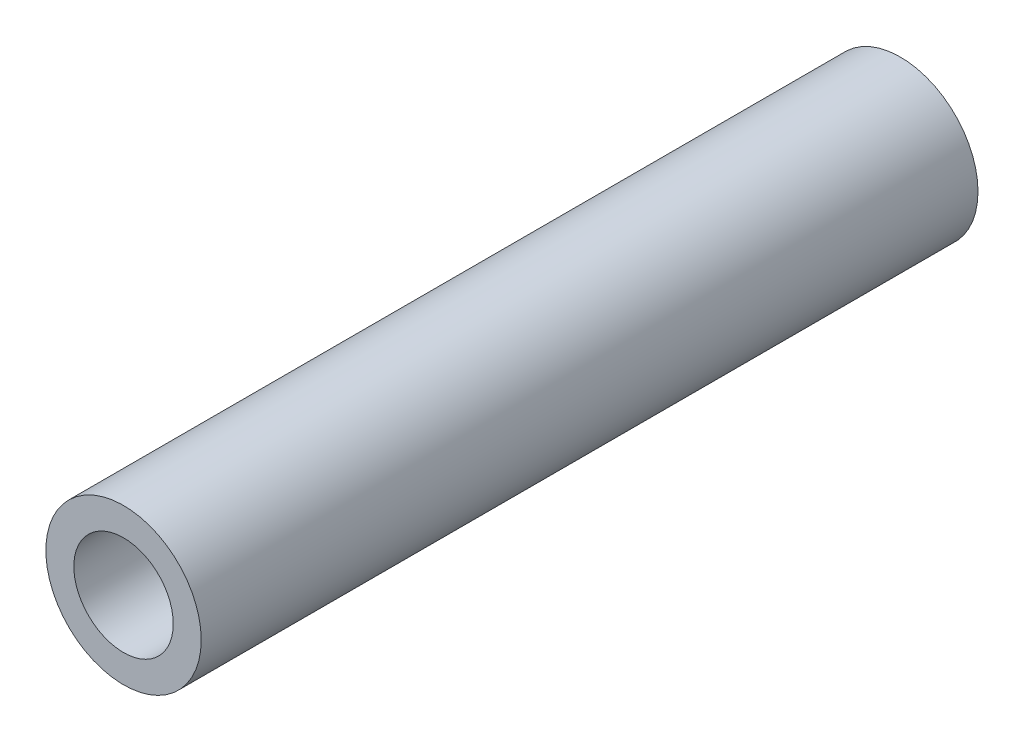
SolidWorks part; units mm, degrees
ref_plane "Front" through (0, 0, 0) normal (0, 0, 1) x (1, 0, 0)
ref_plane "Top" through (0, 0, 0) normal (0, 1, 0) x (1, 0, 0)
ref_plane "Right" through (0, 0, 0) normal (1, 0, 0) x (0, 0, -1)
sketch "Sketch1" plane through (0, 0, 0) normal (0, 0, 1) x (1, 0, 0)
  circle A0 centre (0, 0) radius 1.6
  circle A1 centre (0, 0) radius 2.5
extrude "Boss-Extrude1" add sketch "Sketch1" along normal blind 25
